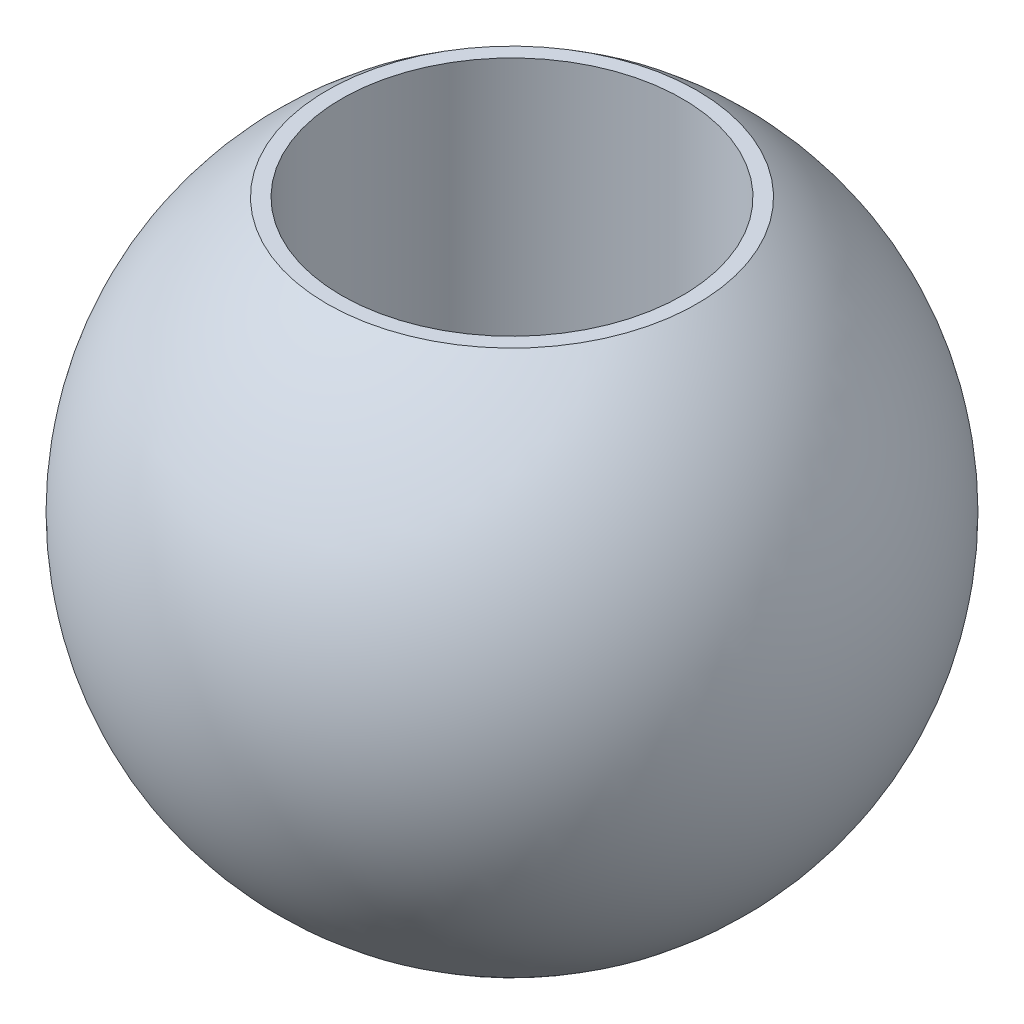
SolidWorks part; units mm, degrees
ref_plane "前视基准面" through (0, 0, 0) normal (0, 0, 1) x (1, 0, 0)
ref_plane "上视基准面" through (0, 0, 0) normal (0, 1, 0) x (1, 0, 0)
ref_plane "右视基准面" through (0, 0, 0) normal (1, 0, 0) x (0, 0, -1)
sketch "草图1" plane through (0, 0, 0) normal (0, 0, 1) x (1, 0, 0)
  line L0 (0, 0) -> (5.8, 0)
  arc A0 (5.8, 0) -> (0, 0) centre (2.9, 0) ccw
  dimension "D1" = 5.8
revolve "旋转1" add sketch "草图1" angle 360 about L0
sketch "草图2" plane through (0, 0, 0) normal (0, 0, 1) x (1, 0, 0)
  line L0 (0, 0) -> (5.8, 0) construction
  line L1 (1.2721, -2.4) -> (4.5279, -2.4)
  line L2 (1.2721, 2.4) -> (4.5279, 2.4)
  line L3 (0, 2.4) -> (5.8, 2.4) construction
  line L4 (0, -2.4) -> (5.8, -2.4) construction
  circle A0 centre (2.9, 0) radius 2.9 construction
  arc A1 (1.2721, -2.4) -> (4.5279, -2.4) centre (2.9, 0) ccw
  arc A2 (4.5279, 2.4) -> (1.2721, 2.4) centre (2.9, 0) ccw
  dimension "D1" = 2.4
  dimension "D2" = 2.4
extrude "切除-拉伸1" cut sketch "草图2" against normal mid plane 10
sketch "草图3" plane through (0, 2.4, 0) normal (0, 1, 0) x (1, 0, 0)
  circle A0 centre (2.9, 0) radius 1.5
  dimension "D1" = 3
extrude "切除-拉伸2" cut sketch "草图3" against normal through all
